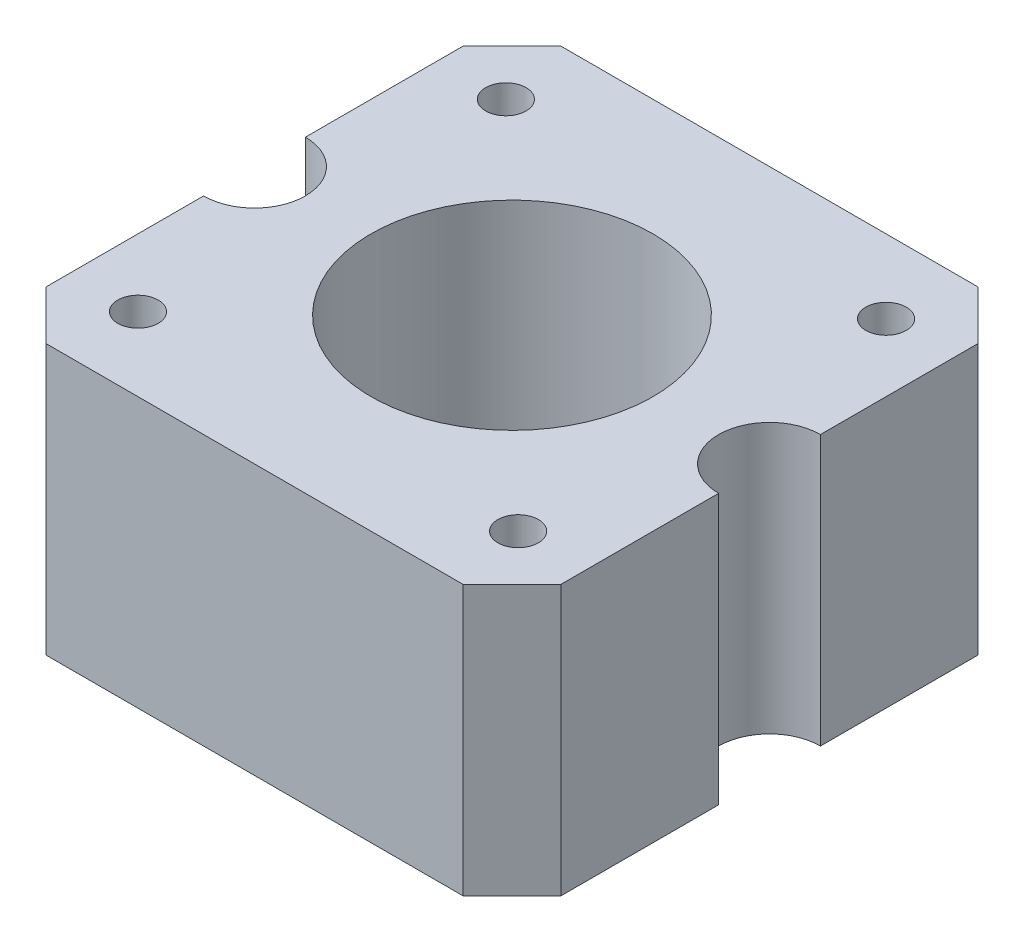
SolidWorks part; units mm, degrees
ref_plane "Front Plane" through (0, 0, 0) normal (0, 0, 1) x (1, 0, 0)
ref_plane "Top Plane" through (0, 0, 0) normal (0, 1, 0) x (1, 0, 0)
ref_plane "Right Plane" through (0, 0, 0) normal (1, 0, 0) x (0, 0, -1)
sketch "Sketch1" plane through (0, 0, 0) normal (0, 1, 0) x (1, 0, 0)
  line L1 (-21, -21) -> (21, -21)
  line L2 (-21, -21) -> (-21, 21)
  line L3 (-21, 21) -> (21, 21)
  line L4 (21, -21) -> (21, 21)
  line L5 (-21, -21) -> (21, 21) construction
  line L6 (-21, 21) -> (21, -21) construction
  point P0 (0, 0)
  dimension "D1" = 42
  dimension "D2" = 42
extrude "Boss-Extrude1" add sketch "Sketch1" along normal blind 22
sketch "Sketch2" plane through (0, 22, 0) normal (0, 1, 0) x (1, 0, 0)
  line L0 (-21, 0) -> (21, 0) construction
  line L1 (-21, 21) -> (-21, -21) construction
  line L2 (21, -21) -> (21, 21) construction
  line L3 (0, -21) -> (0, 21) construction
  line L4 (-21, -21) -> (21, -21) construction
  line L5 (21, 21) -> (-21, 21) construction
  circle A0 centre (0, 0) radius 11.5
  circle A1 centre (-15.5, 15) radius 1.65
  circle A2 centre (15.5, 15) radius 1.65
  circle A3 centre (15.5, -15) radius 1.65
  circle A4 centre (-15.5, -15) radius 1.65
  dimension "D1" = 23
  dimension "D2" = 3.3
  dimension "D3" = 15.5
  dimension "D4" = 15
extrude "Cut-Extrude1" cut sketch "Sketch2" against normal up to next and the other way through all
chamfer "Chamfer1" distance 4 angle 45 4 edges at (-21, 11, 21) (21, 11, 21) (21, 11, -21) (-21, 11, -21)
sketch "Sketch3" plane through (0, 0, 0) normal (0, -1, 0) x (1, 0, 0)
  line L0 (-21, 0) -> (21, 0) construction
  line L1 (-21, -17) -> (-21, 17) construction
  line L2 (21, 17) -> (21, -17) construction
  line L3 (0, 21) -> (0, -21) construction
  line L4 (-17, 21) -> (17, 21) construction
  line L5 (17, -21) -> (-17, -21) construction
  circle A0 centre (-15.5, 15) radius 3
  circle A1 centre (15.5, 15) radius 3
  circle A2 centre (15.5, -15) radius 3
  circle A3 centre (-15.5, -15) radius 3
  dimension "D1" = 6
extrude "Cut-Extrude2" cut sketch "Sketch3" against normal blind 5 and the other way through all
sketch "Sketch4" plane through (0, 22, 0) normal (0, 1, 0) x (1, 0, 0)
  line L0 (0, 21) -> (0, -21) construction
  line L1 (17, 21) -> (-17, 21) construction
  line L2 (-17, -21) -> (17, -21) construction
  line L3 (-21, 17) -> (-21, -17) construction
  circle A0 centre (-21, 0) radius 4.15
  circle A1 centre (21, 0) radius 4.15
  dimension "D1" = 8.3
extrude "Cut-Extrude3" cut sketch "Sketch4" against normal up to next and the other way through all
